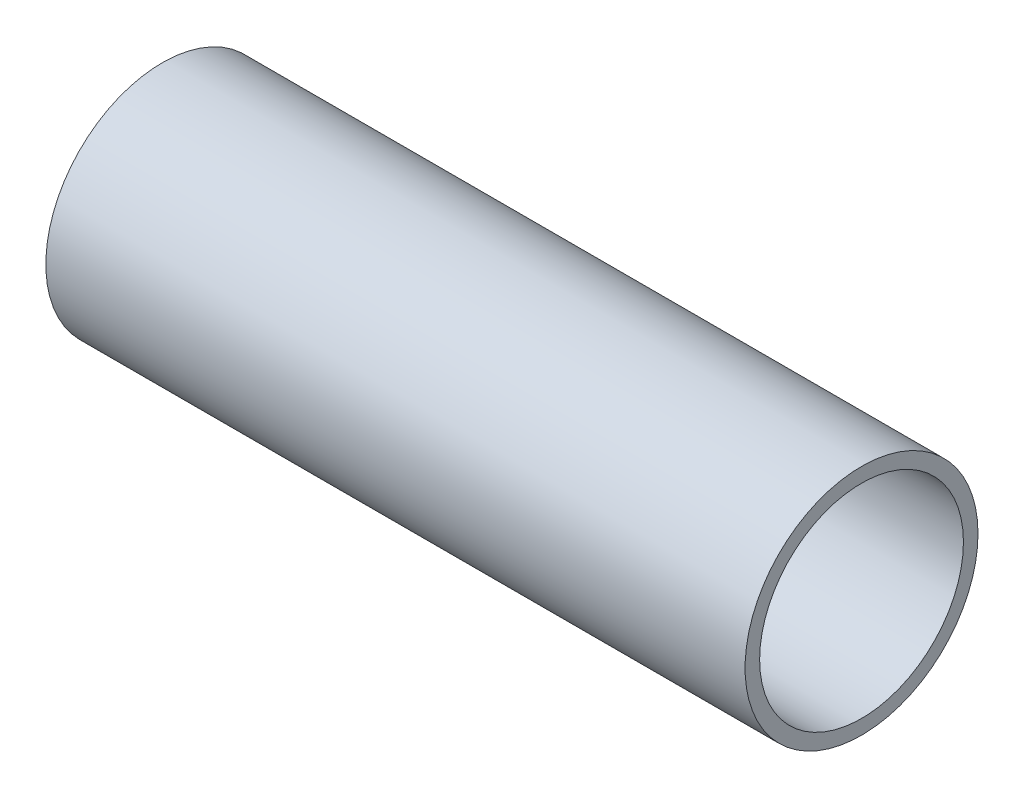
SolidWorks part; units mm, degrees
ref_plane "Front Plane" through (0, 0, 0) normal (0, 0, 1) x (1, 0, 0)
ref_plane "Top Plane" through (0, 0, 0) normal (0, 1, 0) x (1, 0, 0)
ref_plane "Right Plane" through (0, 0, 0) normal (1, 0, 0) x (0, 0, -1)
sketch "Sketch1" plane through (0, 0, 0) normal (1, 0, 0) x (0, 0, -1)
  circle A0 centre (0, 0) radius 44.45
  circle A1 centre (0, 0) radius 50.8
  dimension "D1" = 88.9
  dimension "D2" = 6.35
extrude "Boss-Extrude1" add sketch "Sketch1" along normal blind 305
